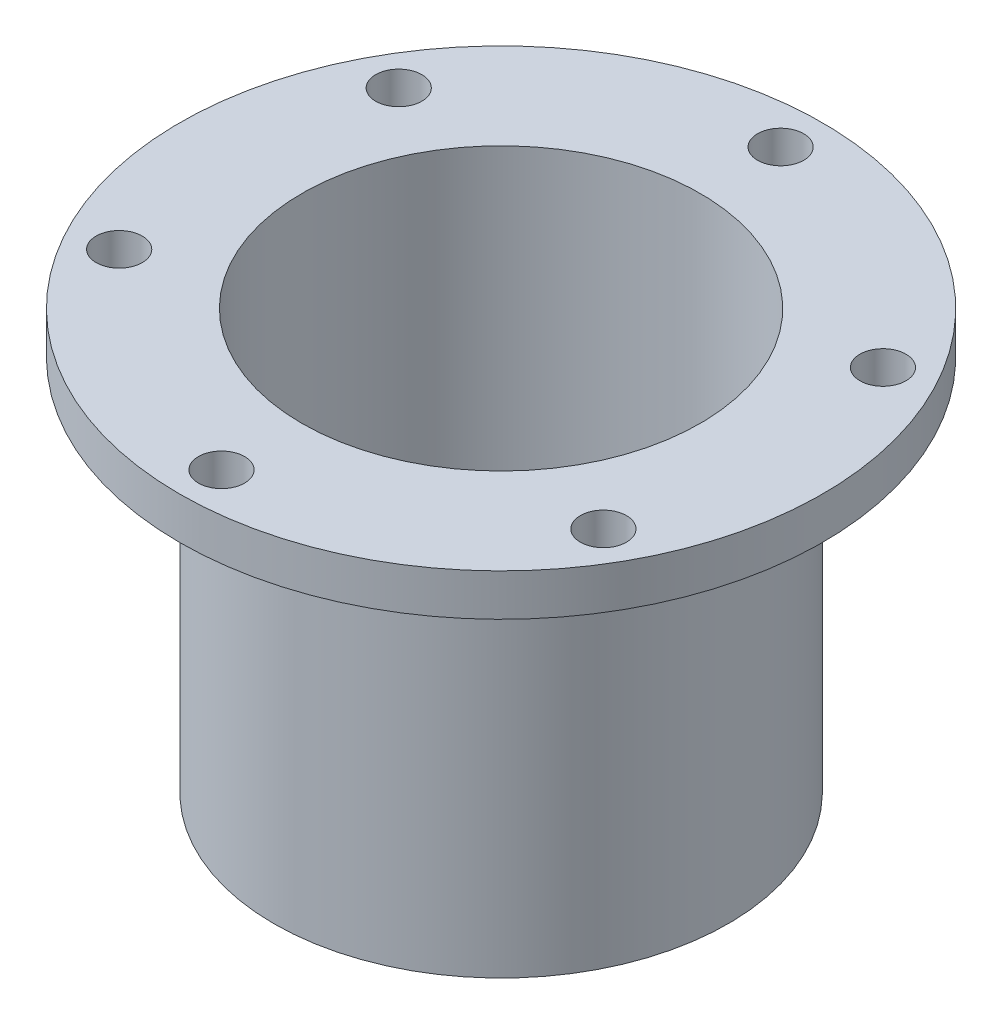
SolidWorks part; units mm, degrees
ref_plane "前视基准面" through (0, 0, 0) normal (0, 0, 1) x (1, 0, 0)
ref_plane "上视基准面" through (0, 0, 0) normal (0, 1, 0) x (1, 0, 0)
ref_plane "右视基准面" through (0, 0, 0) normal (1, 0, 0) x (0, 0, -1)
sketch "草图1" plane through (0, 0, 0) normal (0, 1, 0) x (1, 0, 0)
  circle A0 centre (0, 0) radius 16.25
  dimension "D1" = 32.5
extrude "凸台-拉伸1" add sketch "草图1" along normal blind 27
shell "抽壳1" thickness 2
sketch "草图2" plane through (0, 0, 0) normal (0, -1, 0) x (1, 0, 0)
  line L0 (4.75, 8.2272) -> (0, 0) construction
  line L1 (0, 0) -> (0, 9.5) construction
  circle A0 centre (0, 0) radius 6.75
  circle A1 centre (0, 0) radius 9.5 construction
  circle A2 centre (4.75, 8.2272) radius 1.65
  circle A3 centre (9.5, 0) radius 1.65
  circle A4 centre (4.75, -8.2272) radius 1.65
  circle A5 centre (-4.75, -8.2272) radius 1.65
  circle A6 centre (-9.5, 0) radius 1.65
  circle A7 centre (-4.75, 8.2272) radius 1.65
  point P20 (0, 0)
  dimension "D1" = 13.5
  dimension "D2" = 19
  dimension "D4" = 3.3
  dimension "D3" = 30
  dimension "D5" = 6
extrude "切除-拉伸1" cut sketch "草图2" against normal blind 27
sketch "草图3" plane through (0, 27, 0) normal (0, 1, 0) x (1, 0, 0)
  circle A0 centre (0, 0) radius 14.25
  circle A1 centre (0, 0) radius 23
  circle A2 centre (0, 0) radius 20 construction
  circle A3 centre (0, 20) radius 1.65
  circle A4 centre (17.3205, 10) radius 1.65
  circle A5 centre (17.3205, -10) radius 1.65
  circle A6 centre (0, -20) radius 1.65
  circle A7 centre (-17.3205, -10) radius 1.65
  circle A8 centre (-17.3205, 10) radius 1.65
  point P20 (0, 0)
  dimension "D1" = 28.5
  dimension "D2" = 46
  dimension "D3" = 40
  dimension "D4" = 3.3
  dimension "D5" = 6
extrude "凸台-拉伸2" add sketch "草图3" along normal blind 3
